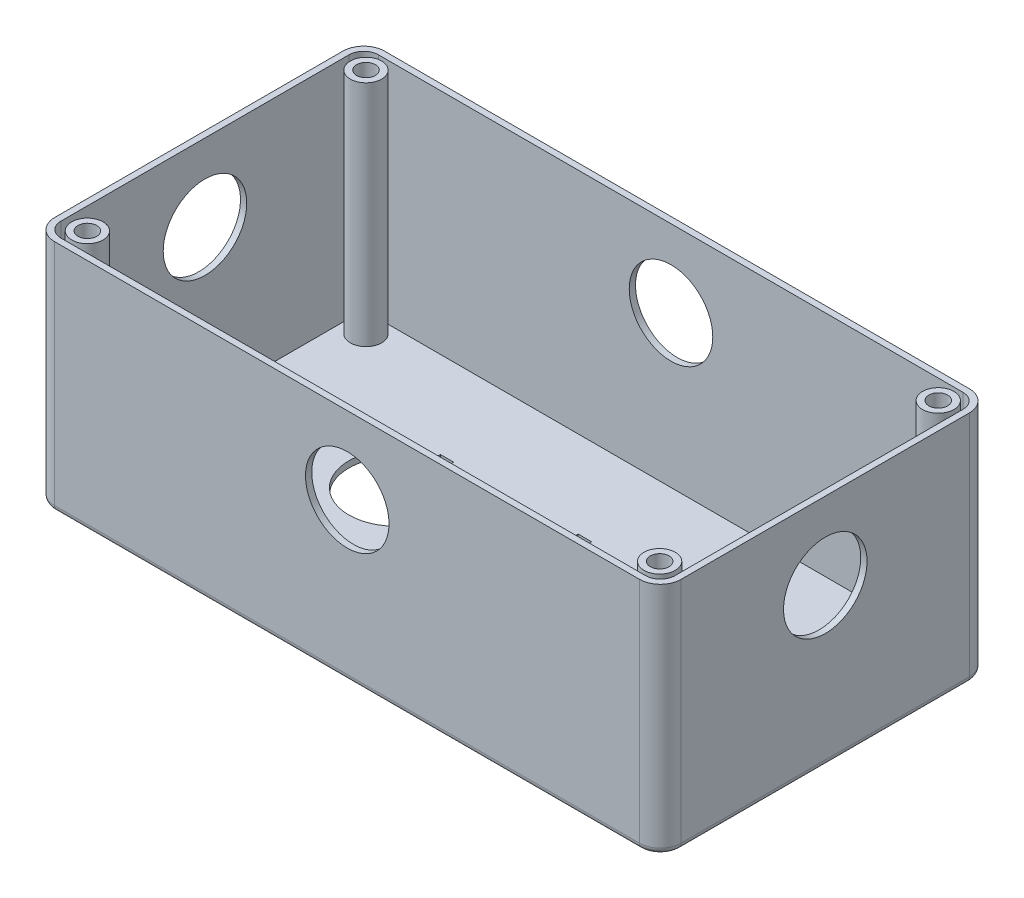
SolidWorks part; units mm, degrees
material "ABS"
ref_plane "Front Plane" through (0, 0, 0) normal (0, 0, 1) x (1, 0, 0)
ref_plane "Top Plane" through (0, 0, 0) normal (0, 1, 0) x (1, 0, 0)
ref_plane "Right Plane" through (0, 0, 0) normal (1, 0, 0) x (0, 0, -1)
sketch "Sketch1" plane through (0, 0, 0) normal (0, 1, 0) x (1, 0, 0)
  line L0 (0, 116.8175) -> (0, -106.793) construction
  line L2 (-34.6, 11.1356) -> (-34.6, 12.25)
  line L3 (-34.6, 12.25) -> (-31.4, 12.25)
  line L4 (-31.4, 11.1356) -> (-31.4, 12.25)
  line L5 (-34.6, 10.25) -> (-31.4, 12.25) construction
  line L6 (-34.6, 12.25) -> (-31.4, 10.25) construction
  line L7 (-70.1931, 34.5) -> (69.8069, 34.5)
  line L8 (-1.6, 11.1356) -> (-1.6, 12.25)
  line L9 (-1.6, 12.25) -> (1.6, 12.25)
  line L10 (1.6, 11.1356) -> (1.6, 12.25)
  line L11 (-1.6, 10.25) -> (1.6, 12.25) construction
  line L12 (-1.6, 12.25) -> (1.6, 10.25) construction
  line L13 (38.4, 11.1356) -> (38.4, 12.25)
  line L14 (38.4, 12.25) -> (41.6, 12.25)
  line L15 (41.6, 11.1356) -> (41.6, 12.25)
  line L16 (38.4, 10.25) -> (41.6, 12.25) construction
  line L17 (38.4, 12.25) -> (41.6, 10.25) construction
  line L18 (-75.1931, 29.5) -> (-75.1931, -39.5)
  line L19 (-70.1931, -44.5) -> (69.8069, -44.5)
  line L20 (74.8069, 29.5) -> (74.8069, -39.5)
  line L21 (-75.1931, 34.5) -> (74.8069, -44.5) construction
  line L22 (-75.1931, -44.5) -> (74.8069, 34.5) construction
  arc A0 (-1.6, 11.1356) -> (1.6, 11.1356) centre (0, 0) ccw
  arc A1 (38.4, 11.1356) -> (41.6, 11.1356) centre (40, 0) ccw
  arc A2 (-34.6, 11.1356) -> (-31.4, 11.1356) centre (-33, 0) ccw
  arc A3 (-70.1931, 34.5) -> (-75.1931, 29.5) centre (-70.1931, 29.5) ccw
  arc A4 (-75.1931, -39.5) -> (-70.1931, -44.5) centre (-70.1931, -39.5) ccw
  arc A5 (69.8069, -44.5) -> (74.8069, -39.5) centre (69.8069, -39.5) ccw
  arc A6 (69.8069, 34.5) -> (74.8069, 29.5) centre (69.8069, 29.5) cw
  circle A7 centre (68.5, 28.35) radius 2.25
  circle A8 centre (68.5, -38.35) radius 2.25
  circle A9 centre (-68.5, -38.35) radius 2.25
  circle A10 centre (-68.5, 28.35) radius 2.25
  point P0 (0, 0)
  point P1 (-33, 11.25)
  point P7 (40, 11.25)
  point P16 (0, 11.25)
  dimension "D1" = 22.5
  dimension "D2" = 22.5
  dimension "D3" = 22.5
  dimension "D15" = 5
  dimension "D16" = 4.5
  dimension "D17" = 4.5
  dimension "D4" = 33
  dimension "D5" = 40
  dimension "D6" = 2
  dimension "D7" = 3.2
  dimension "D8" = 3.2
  dimension "D9" = 2
  dimension "D10" = 3.2
  dimension "D11" = 2
  dimension "D12" = 150
  dimension "D13" = 79
  dimension "D14" = 34.5
  dimension "D18" = 66.7
  dimension "D19" = 6.15
  dimension "D20" = 137
extrude "Boss-Extrude1" add sketch "Sketch1" along normal blind 56.2
shell "Shell1" thickness 1.5
sketch "Sketch2" plane through (0, 56.2, 0) normal (0, 1, 0) x (1, 0, 0)
  line L1 (-53.7633, -21.8294) -> (53.7633, -21.8294)
  line L2 (-53.7633, -21.8294) -> (-53.7633, 21.8294)
  line L3 (-53.7633, 21.8294) -> (53.7633, 21.8294)
  line L4 (53.7633, -21.8294) -> (53.7633, 21.8294)
  line L5 (-53.7633, -21.8294) -> (53.7633, 21.8294) construction
  line L6 (-53.7633, 21.8294) -> (53.7633, -21.8294) construction
  point P0 (0, 0)
extrude "Cut-Extrude1" cut sketch "Sketch2" against normal blind 54.7
fillet "Fillet1" radius 1.5 8 edges at (-0.1931, 0, 44.5) (-73.7286, 0, 43.0355) (-75.1931, 0, 5) (-73.7286, 0, -33.0355) (-0.1931, 0, -34.5) (73.3424, 0, -33.0355) (74.8069, 0, 5) (73.3424, 0, 43.0355)
sketch "Sketch3" plane through (0, 0, -34.5) normal (0, 0, -1) x (-1, 0, 0)
  line L0 (0, 0) -> (0.1931, 56.2) construction
  line L1 (-69.8069, 56.2) -> (70.1931, 56.2) construction
  line L2 (-74.8069, 28.85) -> (75.1931, 28.85) construction
  line L3 (-74.8069, 56.2) -> (-74.8069, 1.5) construction
  line L4 (75.1931, 56.2) -> (75.1931, 1.5) construction
  circle A0 centre (0.1295, 37.7) radius 10
  dimension "D2" = 20
  dimension "D1" = 18.5
extrude "Cut-Extrude2" cut sketch "Sketch3" against normal through all
sketch "Sketch4" plane through (-75.1931, 0, 0) normal (-1, 0, 0) x (0, 0, 1)
  line L0 (5, 56.2) -> (5, 0) construction
  line L1 (-29.5, 56.2) -> (39.5, 56.2) construction
  line L2 (39.5, 0) -> (-29.5, 0) construction
  circle A0 centre (5, 37.7) radius 10
  dimension "D1" = 20
  dimension "D2" = 18.5
extrude "Cut-Extrude3" cut sketch "Sketch4" against normal through all
sketch "Sketch6" plane through (0, 0, 0) normal (0, -1, 0) x (1, 0, 0)
  line L0 (-33, 0) -> (-33, 48.6988) construction
  line L1 (0, 0) -> (0, 61.7) construction
  line L2 (40, 8) -> (40, 43) construction
  line L3 (-68.5, 38.35) -> (68.5, 38.35) construction
  line L4 (69.8069, 43) -> (-70.1931, 43) construction
  line L5 (-44.25, 23.35) -> (-21.75, 23.35)
  line L6 (-44.25, 23.35) -> (-44.25, 38.35)
  line L7 (-44.25, 38.35) -> (-21.75, 38.35)
  line L8 (-21.75, 23.35) -> (-21.75, 38.35)
  line L9 (-44.25, 23.35) -> (-21.75, 38.35) construction
  line L10 (-44.25, 38.35) -> (-21.75, 23.35) construction
  line L12 (51.25, 23.35) -> (28.75, 23.35)
  line L13 (51.25, 23.35) -> (51.25, 38.35)
  line L14 (51.25, 38.35) -> (28.75, 38.35)
  line L15 (28.75, 23.35) -> (28.75, 38.35)
  line L16 (51.25, 23.35) -> (28.75, 38.35) construction
  line L17 (-11.25, 23.35) -> (11.25, 23.35)
  line L18 (-11.25, 23.35) -> (-11.25, 38.35)
  line L19 (-11.25, 38.35) -> (11.25, 38.35)
  line L20 (11.25, 23.35) -> (11.25, 38.35)
  line L21 (-11.25, 23.35) -> (11.25, 38.35) construction
  line L22 (-11.25, 38.35) -> (11.25, 23.35) construction
  line L23 (51.25, 38.35) -> (28.75, 23.35) construction
  circle A0 centre (40, 6.5) radius 1.5 construction
  point P13 (-33, 30.85)
  point P22 (40, 30.85)
  point P23 (0, 30.85)
  point P28 (40, 30.85)
  dimension "D1" = 22.5
  dimension "D2" = 15
  dimension "D3" = 22.5
  dimension "D4" = 15
  dimension "D5" = 22.5
  dimension "D6" = 15
  dimension "D7" = 11.25
  dimension "D8" = 40
  dimension "D9" = 19.65
  dimension "D10" = 19.65
extrude "Cut-Extrude5" cut sketch "Sketch6" against normal blind 0.25
